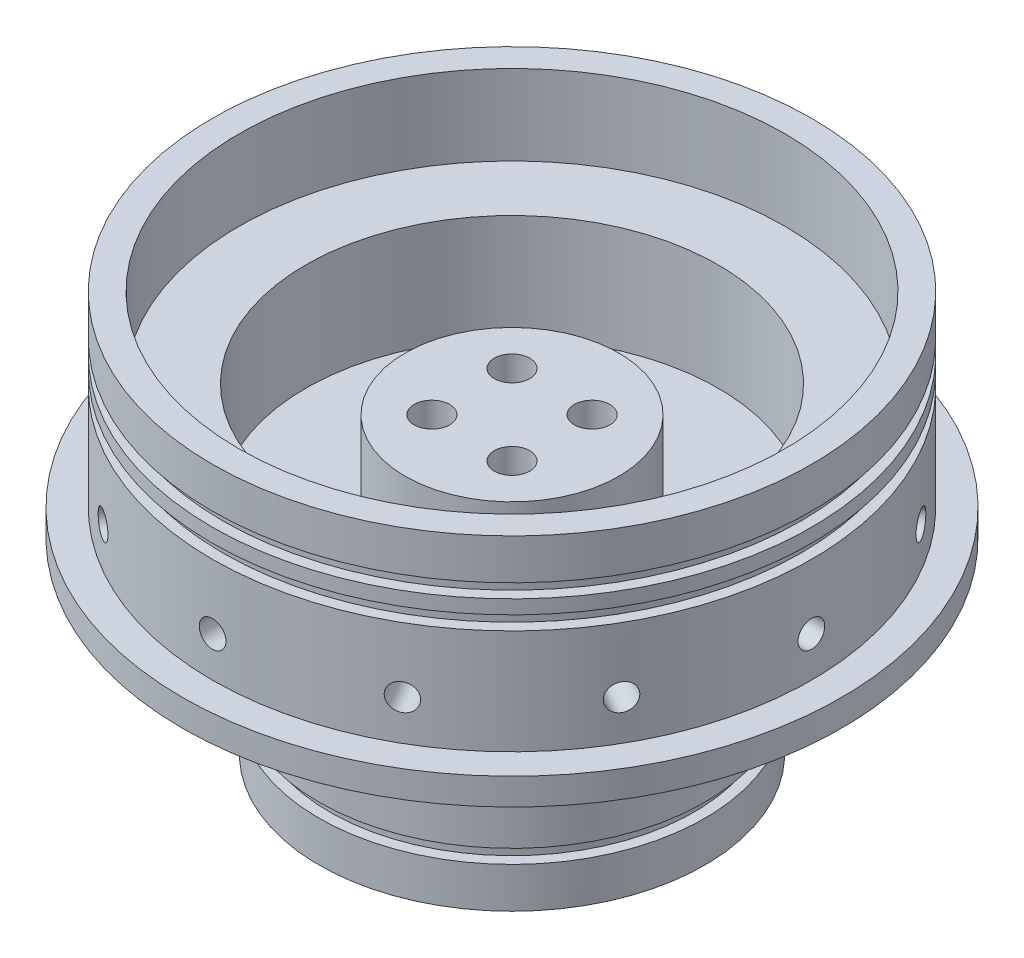
SolidWorks part; units mm, degrees
material "6061-T6 (SS)"
ref_plane "Front Plane" through (0, 0, 0) normal (0, 0, 1) x (1, 0, 0)
ref_plane "Top Plane" through (0, 0, 0) normal (0, 1, 0) x (1, 0, 0)
ref_plane "Right Plane" through (0, 0, 0) normal (1, 0, 0) x (0, 0, -1)
sketch "Sketch1" plane through (0, 0, 0) normal (0, 1, 0) x (1, 0, 0)
  circle A0 centre (0, 0) radius 78.359
extrude "BulkheadPlate" add sketch "Sketch1" along normal blind 6.35 contours A0
sketch "Sketch3" plane through (0, 6.35, 0) normal (0, 1, 0) x (1, 0, 0)
  circle A0 centre (0, 0) radius 71.247
  circle A1 centre (0, 0) radius 49.022
extrude "NosBase" add sketch "Sketch3" along normal blind 25.4
sketch "Sketch4" plane through (0, 31.75, 0) normal (0, 1, 0) x (1, 0, 0)
  circle A0 centre (0, 0) radius 64.897
  circle A1 centre (0, 0) radius 71.247
extrude "NosORings" add sketch "Sketch4" along normal blind 19.05
sketch "Sketch5" plane through (0, 0, 0) normal (0, -1, 0) x (1, 0, 0)
  circle A0 centre (0, 0) radius 45.847
  circle A1 centre (0, 0) radius 23.622
extrude "EngineBase" add sketch "Sketch5" along normal blind 25.4
sketch "Sketch6" plane through (0, -25.4, 0) normal (0, -1, 0) x (-1, 0, 0)
  circle A0 centre (0, 0) radius 39.497
  circle A1 centre (0, 0) radius 45.847
extrude "EngineORings" add sketch "Sketch6" along normal blind 19.05
sketch3d "3DSketch2" plane through (0, 0, 0) normal (0, 0, 1) x (1, 0, 0)
sketch "Sketch7" plane through (0, 0, 71.247) normal (0, 0, 1) x (1, 0, 0)
  line L0 (0, 6.2398) -> (0, 15.8918)
  circle A0 centre (0, 15.8918) radius 3.175
extrude "NosBoltHole" cut sketch "Sketch7" against normal blind 12.7
sketch "Sketch9" plane through (0, 0, 0) normal (0, 0, 1) x (1, 0, 0)
  line L0 (0, 0) -> (0, 72.7405)
pattern_circular "NosBoltHoles" count 12 over 360 about axis through (0, 0, 0) along (0, 1, 0) of "NosBoltHole"
sketch "Sketch13" plane through (0, 0, 0) normal (0, 0, 1) x (1, 0, 0)
  line L0 (0, 0) -> (0, 50.8)
  line L1 (0, 50.8) -> (-71.247, 50.8)
  line L2 (-71.247, 50.8) -> (-71.247, 6.35)
  line L3 (-71.247, 50.8) -> (-71.247, 41.148)
  line L4 (-71.247, 41.148) -> (-68.707, 41.148)
  line L5 (-68.707, 41.148) -> (-68.707, 37.846)
  line L6 (-68.707, 37.846) -> (-71.247, 37.846)
  line L7 (-71.247, 37.846) -> (-71.247, 34.544)
  line L8 (-71.247, 34.544) -> (-68.707, 34.544)
  line L9 (-68.707, 34.544) -> (-68.707, 31.242)
  line L10 (-68.707, 31.242) -> (-71.247, 31.242)
revolve "NosORingChannel" cut sketch "Sketch13" angle 360 about L0
sketch3d "3DSketch3" plane through (0, 0, 0) normal (0, 0, 1) x (1, 0, 0)
sketch "Sketch11" plane through (0, 0, 45.847) normal (0, 0, 1) x (1, 0, 0)
  circle A0 centre (0, -7.62) radius 2.413
extrude "EngineBoltHole" cut sketch "Sketch11" against normal blind 12.7
pattern_circular "EngineBoltHoles" count 12 over 360 about axis through (0, 0, 0) along (0, 1, 0) of "EngineBoltHole"
sketch "Sketch12" plane through (0, 0, 0) normal (0, 0, 1) x (1, 0, 0)
  line L0 (0, 0) -> (0, -44.45)
  line L1 (0, -44.45) -> (-45.847, -44.45)
  line L2 (-45.847, 0) -> (-45.847, -44.45)
  line L3 (-45.847, -10.033) -> (-45.847, -44.45) construction
  line L4 (-45.847, -34.798) -> (-43.307, -34.798)
  line L5 (-43.307, -34.798) -> (-43.307, -31.496)
  line L6 (-43.307, -31.496) -> (-45.847, -31.496)
  line L8 (-45.847, -34.798) -> (-45.847, -31.496)
revolve "EngineORingChannel" cut sketch "Sketch12" angle 360 about L0
sketch "Sketch14" plane through (0, 0, 0) normal (0, -1, 0) x (1, 0, 0)
  point P9 (-9.525, 9.525)
  point P10 (9.525, 9.525)
  point P11 (9.525, -9.525)
  point P12 (-9.525, -9.525)
sketch "Sketch17" plane through (0, 6.35, 0) normal (0, 1, 0) x (1, 0, 0)
  circle A0 centre (0, 0) radius 25.4
extrude "InjectorManifold" add sketch "Sketch17" along normal blind 19.05
sketch "Sketch18" plane through (0, 25.4, 0) normal (0, 1, 0) x (1, 0, 0)
  point P0 (-9.525, 9.525)
  point P1 (9.525, 9.525)
  point P3 (9.525, -9.525)
  point P5 (-9.525, -9.525)
hole_wizard "InjectorTaps" positions "Sketch15" profile "Sketch16" hole size "1/8" standard "ANSI Inch"
sketch "Sketch15" plane through (0, 0, 0) normal (0, -1, 0) x (-1, 0, 0)
  point P0 (-9.525, 9.525)
  point P3 (9.525, 9.525)
  point P6 (9.525, -9.525)
  point P9 (-9.525, -9.525)
sketch "Sketch16" plane through (9.525, 0, -9.525) normal (1, 0, 0) x (0, 0, -1)
  line L0 (0, 0) -> (0, 15.2335)
  line L1 (0, 15.2335) -> (4.2164, 12.7)
  line L2 (4.2164, 12.7) -> (4.2164, 0)
  line L5 (4.2164, 0) -> (0, 0)
  line L10 (0, 15.2335) -> (-4.2164, 12.7) construction
  line L11 (0, -6.35) -> (0, 107.95) construction
  dimension "Hole Dia." = 8.4328
  dimension "Hole Depth" = 12.7
  dimension "Drill Angle" = 118
hole_wizard "CNVATaps" positions "Sketch19" profile "Sketch20" hole size "1/8" standard "ANSI Inch"
sketch "Sketch19" plane through (0, 25.4, 0) normal (0, 1, 0) x (1, 0, 0)
  point P0 (-9.525, 9.525)
  point P3 (9.525, 9.525)
  point P6 (9.525, -9.525)
  point P9 (-9.525, -9.525)
sketch "Sketch20" plane through (-9.525, 25.4, -9.525) normal (1, 0, 0) x (0, 0, 1)
  line L0 (0, 0) -> (0, 15.2335)
  line L1 (0, 15.2335) -> (4.2164, 12.7)
  line L2 (4.2164, 12.7) -> (4.2164, 0)
  line L5 (4.2164, 0) -> (0, 0)
  line L10 (0, 15.2335) -> (-4.2164, 12.7) construction
  line L11 (0, -6.35) -> (0, 107.95) construction
  dimension "Hole Dia." = 8.4328
  dimension "Hole Depth" = 12.7
  dimension "Drill Angle" = 118
